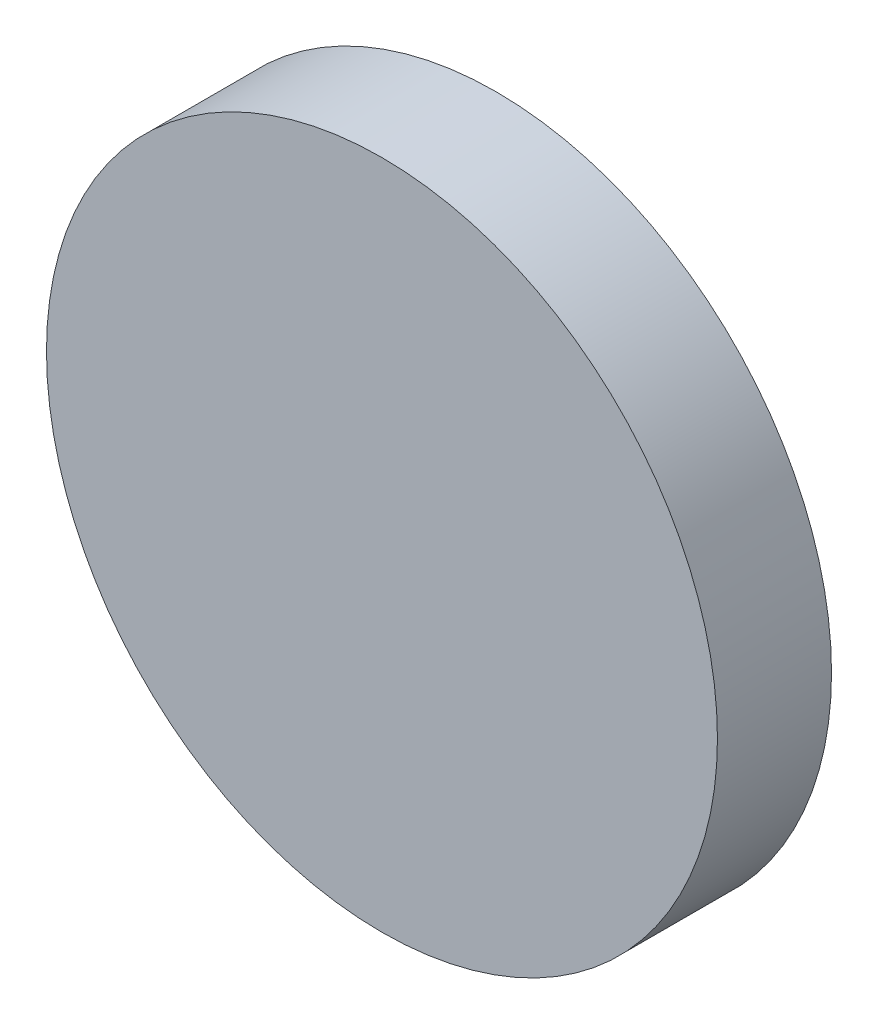
SolidWorks part; units mm, degrees
ref_plane "Front Plane" through (0, 0, 0) normal (0, 0, 1) x (1, 0, 0)
ref_plane "Top Plane" through (0, 0, 0) normal (0, 1, 0) x (1, 0, 0)
ref_plane "Right Plane" through (0, 0, 0) normal (1, 0, 0) x (0, 0, -1)
sketch "Sketch1" plane through (0, 0, 0) normal (0, 0, 1) x (1, 0, 0)
  circle A0 centre (0, 0) radius 25
  dimension "D1" = 50
extrude "Boss-Extrude1" add sketch "Sketch1" along normal blind 8.5
sketch "Sketch2" plane through (0, 0, 0) normal (0, 0, -1) x (-1, 0, 0)
  circle A0 centre (0, 0) radius 6
  circle A1 centre (0, 0) radius 2.5
  dimension "D1" = 5
  dimension "D2" = 12
extrude "Boss-Extrude2" add sketch "Sketch2" along normal blind 10
